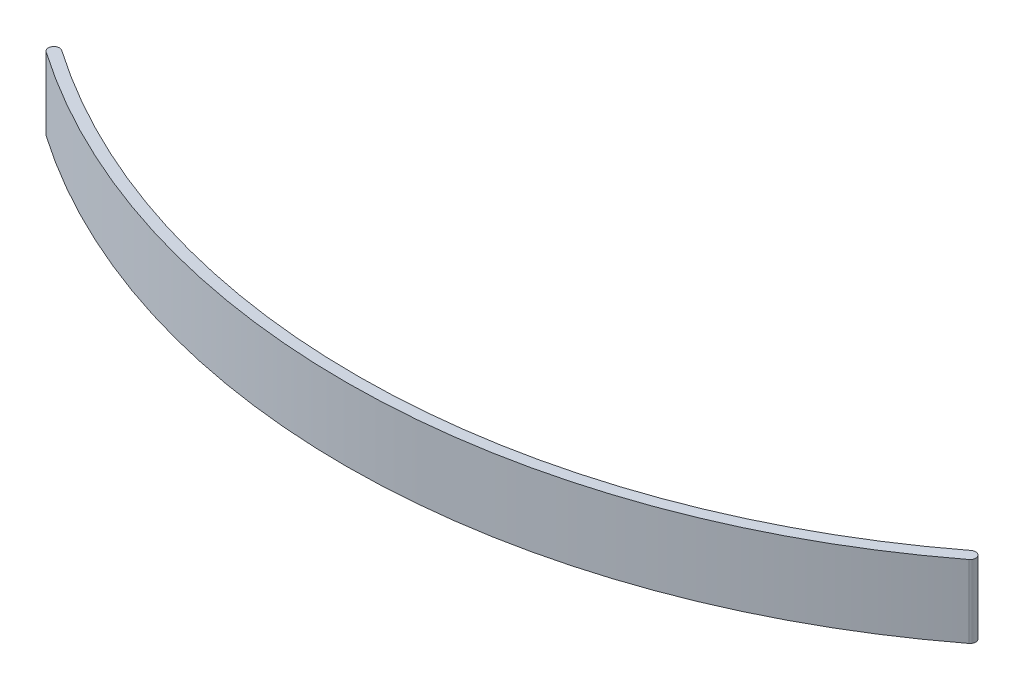
SolidWorks part; units mm, degrees
ref_plane "Front Plane" through (0, 0, 0) normal (0, 0, 1) x (1, 0, 0)
ref_plane "Top Plane" through (0, 0, 0) normal (0, 1, 0) x (1, 0, 0)
ref_plane "Right Plane" through (0, 0, 0) normal (1, 0, 0) x (0, 0, -1)
sketch "Sketch1" plane through (0, 0, 0) normal (0, 1, 0) x (1, 0, 0)
  arc A0 (39.6723, 14) -> (-40.3042, 12.0611) centre (-1.6455, 67.8735) cw
  arc A1 (39.6723, 14) -> (-40.3042, 12.0611) centre (-1.6455, 67.8735) cw construction
  arc A2 (-40.5889, 11.65) -> (39.9766, 13.6032) centre (-1.6455, 67.8735) ccw
  arc A3 (-40.0195, 12.4721) -> (39.3681, 14.3968) centre (-1.6455, 67.8735) ccw
  arc A4 (-40.0195, 12.4721) -> (-40.5889, 11.65) centre (-40.3042, 12.0611) ccw
  arc A5 (39.9766, 13.6032) -> (39.3681, 14.3968) centre (39.6723, 14) ccw
  point P3 (0, 0)
  point P5 (0, 0)
  dimension "D3" = 1
  dimension "D1" = 80
  dimension "D2" = 14
extrude "Boss-Extrude1" add sketch "Sketch1" along normal blind 6.5
